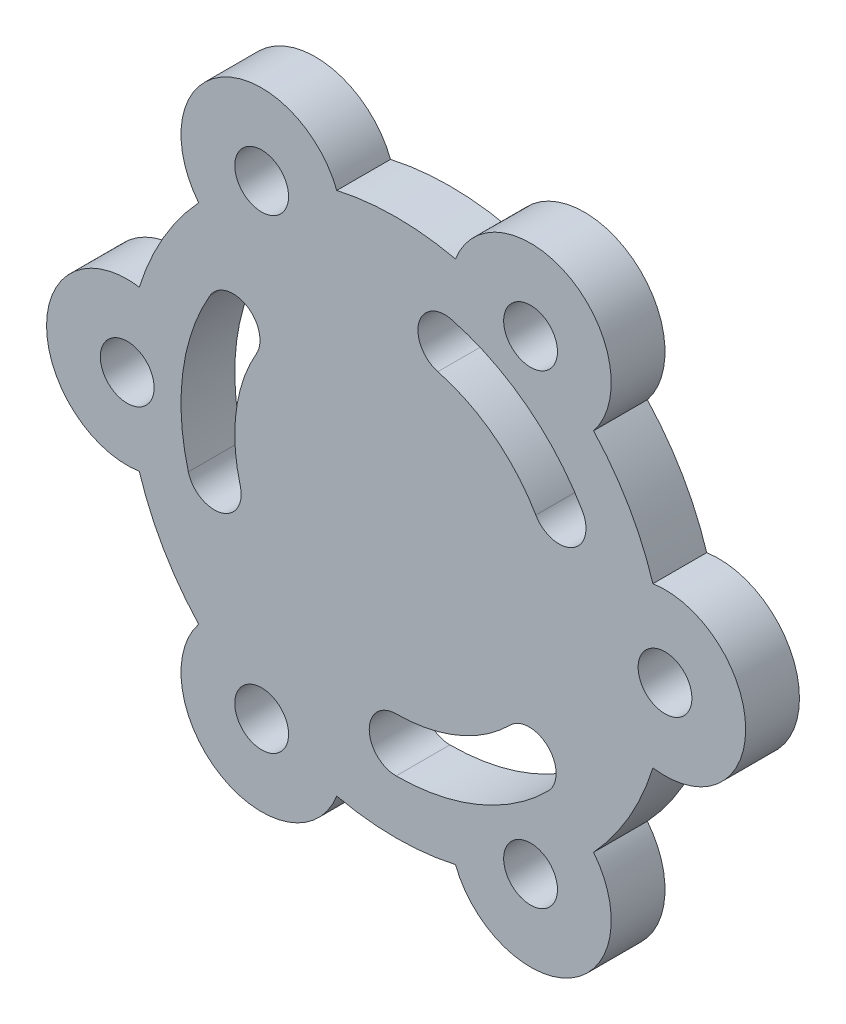
SolidWorks part; units mm, degrees
ref_plane "Front Plane" through (0, 0, 0) normal (0, 0, 1) x (1, 0, 0)
ref_plane "Top Plane" through (0, 0, 0) normal (0, 1, 0) x (1, 0, 0)
ref_plane "Right Plane" through (0, 0, 0) normal (1, 0, 0) x (0, 0, -1)
sketch "Sketch1" plane through (0, 0, 0) normal (0, 0, 1) x (1, 0, 0)
  line L0 (-65, 0) -> (65, 0) construction
  line L1 (0, 0) -> (30.3109, 17.5) construction
  circle A1 centre (-50, 0) radius 5
  arc A2 (-47.75, 14.8303) -> (-47.75, -14.8303) centre (-50, 0) ccw
  circle A3 centre (-50, 0) radius 15 construction
  arc A4 (-47.75, -14.8303) -> (-36.7184, -33.9376) centre (0, 0) ccw
  circle A5 centre (-25, 43.3013) radius 5
  circle A6 centre (25, 43.3013) radius 5
  circle A7 centre (50, 0) radius 5
  circle A8 centre (25, -43.3013) radius 5
  circle A9 centre (-25, -43.3013) radius 5
  arc A10 (-11.0316, 48.7679) -> (-36.7184, 33.9376) centre (-25, 43.3013) ccw
  arc A11 (36.7184, 33.9376) -> (11.0316, 48.7679) centre (25, 43.3013) ccw
  arc A12 (47.75, -14.8303) -> (47.75, 14.8303) centre (50, 0) ccw
  arc A13 (11.0316, -48.7679) -> (36.7184, -33.9376) centre (25, -43.3013) ccw
  arc A14 (-36.7184, -33.9376) -> (-11.0316, -48.7679) centre (-25, -43.3013) ccw
  arc A15 (-36.7184, 33.9376) -> (-47.75, 14.8303) centre (0, 0) ccw
  arc A16 (11.0316, 48.7679) -> (-11.0316, 48.7679) centre (0, 0) ccw
  arc A17 (47.75, 14.8303) -> (36.7184, 33.9376) centre (0, 0) ccw
  arc A18 (-11.0316, -48.7679) -> (11.0316, -48.7679) centre (0, 0) ccw
  arc A19 (-29.1997, -40.5879) -> (-20.5503, -45.5816) centre (0, 0) ccw
  arc A20 (30.3109, 17.5) -> (9.0587, 33.8074) centre (0, 0) ccw construction
  arc A21 (36.7184, -33.9376) -> (47.75, -14.8303) centre (0, 0) ccw
  arc A22 (34.641, 20) -> (10.3528, 38.637) centre (0, 0) ccw
  arc A23 (25.9808, 15) -> (7.7646, 28.9778) centre (0, 0) ccw
  arc A24 (25.9808, 15) -> (34.641, 20) centre (30.3109, 17.5) ccw
  arc A25 (10.3528, 38.637) -> (7.7646, 28.9778) centre (9.0587, 33.8074) ccw
  arc A26 (0, -35) -> (24.7487, -24.7487) centre (0, 0) ccw construction
  arc A27 (0, -40) -> (28.2843, -28.2843) centre (0, 0) ccw
  arc A28 (0, -30) -> (21.2132, -21.2132) centre (0, 0) ccw
  arc A29 (0, -30) -> (0, -40) centre (0, -35) ccw
  arc A30 (28.2843, -28.2843) -> (21.2132, -21.2132) centre (24.7487, -24.7487) ccw
  arc A31 (-30.3109, 17.5) -> (-33.8074, -9.0587) centre (0, 0) ccw construction
  arc A32 (-34.641, 20) -> (-38.637, -10.3528) centre (0, 0) ccw
  arc A33 (-25.9808, 15) -> (-28.9778, -7.7646) centre (0, 0) ccw
  arc A34 (-25.9808, 15) -> (-34.641, 20) centre (-30.3109, 17.5) ccw
  arc A35 (-38.637, -10.3528) -> (-28.9778, -7.7646) centre (-33.8074, -9.0587) ccw
  point P21 (0, 0)
  point P37 (0, 0)
  point P38 (21.3067, 27.7674)
  point P46 (0, 0)
  point P53 (13.3939, -32.3358)
  point P60 (-34.7006, 4.5684)
  point P65 (0, 0)
  dimension "D3" = 50
  dimension "D4" = 10
  dimension "D10" = 35
  dimension "D11" = 5
  dimension "D2" = 3
  dimension "D8" = 45
  dimension "D9" = 30
  dimension "D5" = 10
  dimension "D6" = 6
  dimension "D7" = 6
extrude "Boss-Extrude1" add sketch "Sketch1" along normal blind 10 contours A13 A21 A12 A17 A11 A16 A10 A15 A2 A4 A14 A18 A35 A32 A34 A33 A30 A27 A29 A28 A25 A22 A24 A23 A1 A5 A6 A7 A8 A9
